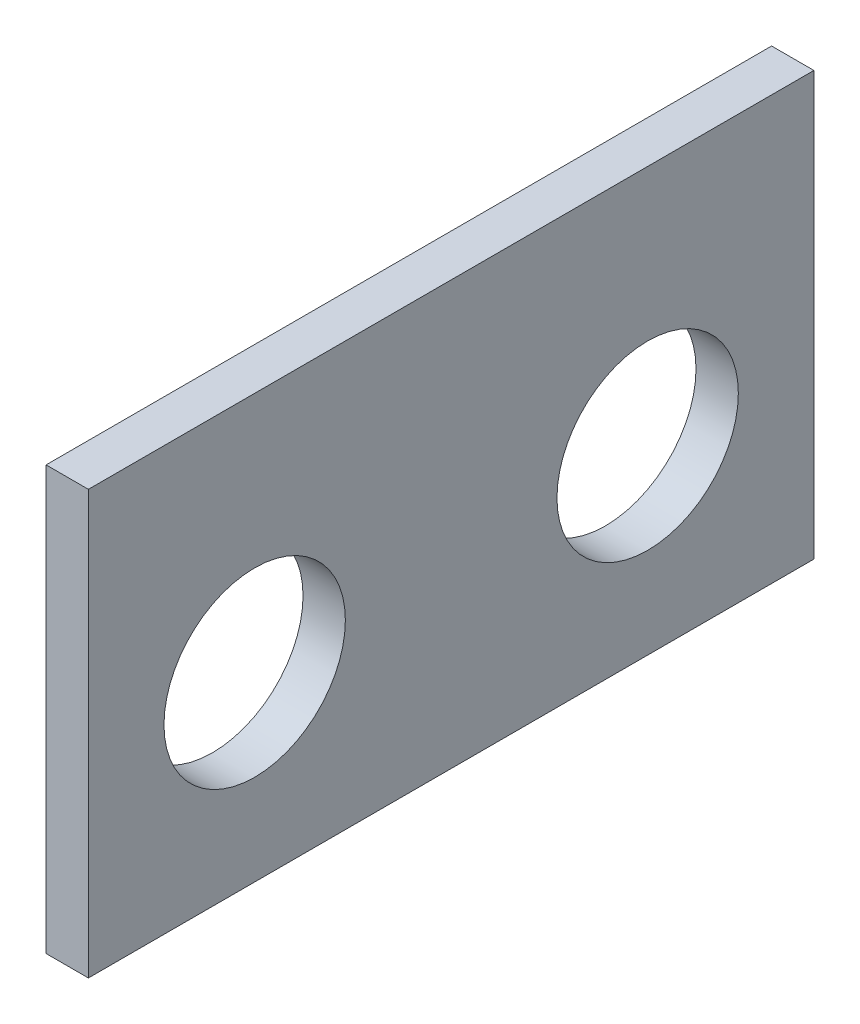
SolidWorks part; units mm, degrees
ref_plane "前视基准面" through (0, 0, 0) normal (0, 0, 1) x (1, 0, 0)
ref_plane "上视基准面" through (0, 0, 0) normal (0, 1, 0) x (1, 0, 0)
ref_plane "右视基准面" through (0, 0, 0) normal (1, 0, 0) x (0, 0, -1)
other "Configuration Table"
sketch "草图1" plane through (0, 0, 0) normal (1, 0, 0) x (0, 0, -1)
  line L2 (172.9638, 67.5747) -> (172.9638, 60.5747)
  line L3 (172.9638, 60.5747) -> (160.9638, 60.5747)
  line L4 (160.9638, 67.5747) -> (160.9638, 60.5747)
  line L9 (172.9638, 67.5747) -> (160.9638, 67.5747)
  circle A0 centre (170.2138, 63.5747) radius 1.5
  circle A1 centre (163.7138, 63.5747) radius 1.5
  dimension "D5" = 3
  dimension "D6" = 3
  dimension "D1" = 12
  dimension "D2" = 7
  dimension "D3" = 4
  dimension "D4" = 4
  dimension "D9" = 6.5
  dimension "D10" = 2.75
extrude "凸台-拉伸1" add sketch "草图1" along normal blind 0.7 contours L4 L3 L2 L9 | A0 | A1
